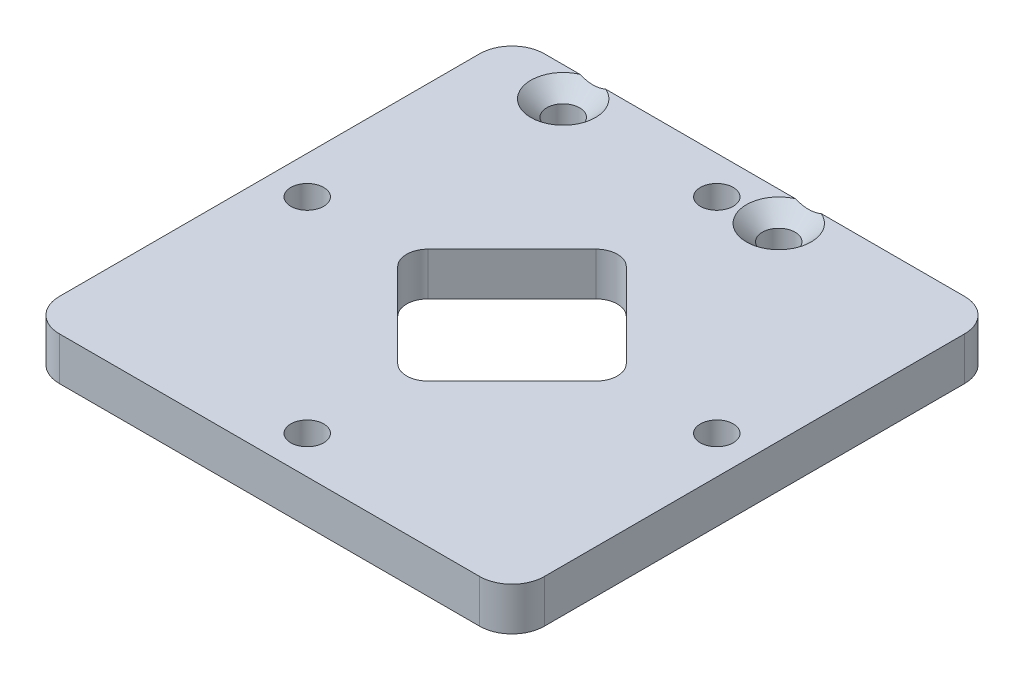
SolidWorks part; units mm, degrees
material "Thornel Mat VMA"
ref_plane "前视基准面" through (0, 0, 0) normal (0, 0, 1) x (1, 0, 0)
ref_plane "上视基准面" through (0, 0, 0) normal (0, 1, 0) x (1, 0, 0)
ref_plane "右视基准面" through (0, 0, 0) normal (1, 0, 0) x (0, 0, -1)
other "Configuration Table"
sketch "草图1" plane through (0, 0, 0) normal (0, 1, 0) x (1, 0, 0)
  line L1 (-22.5, -22.5) -> (22.5, -22.5)
  line L2 (-22.5, -22.5) -> (-22.5, 22.5)
  line L3 (-22.5, 22.5) -> (22.5, 22.5)
  line L4 (22.5, -22.5) -> (22.5, 22.5)
  line L5 (-22.5, -22.5) -> (22.5, 22.5) construction
  line L6 (-22.5, 22.5) -> (22.5, -22.5) construction
  point P0 (0, 0)
  dimension "D1" = 45
  dimension "D2" = 45
extrude "凸台-拉伸1" add sketch "草图1" along normal blind 4
sketch "草图2" plane through (0, 4, 0) normal (0, 1, 0) x (1, 0, 0)
  line L0 (0, 0) -> (0, -22.5) construction
  line L1 (-22.5, -22.5) -> (22.5, -22.5) construction
  circle A0 centre (-19, 0) radius 1.525
  circle A1 centre (19, 0) radius 1.525
  dimension "D1" = 3.05
  dimension "D2" = 38
extrude "切除-拉伸1" cut sketch "草图2" against normal blind 4
fillet "圆角1" radius 3 4 edges at (-22.5, 2, 22.5) (-22.5, 2, -22.5) (22.5, 2, -22.5) (22.5, 2, 22.5)
sketch "草图3" plane through (0, 4, 0) normal (0, 1, 0) x (1, 0, 0)
  circle A0 centre (5, 19.75) radius 1.525
  circle A1 centre (-15, 19.75) radius 1.525
  circle A2 centre (-15, 19.75) radius 1.25 construction
  circle A3 centre (5, 19.75) radius 1.25 construction
  dimension "D1" = 3.05
hole_wizard "孔1" positions "3D草图1" profile "草图4" legacy end condition through all
sketch3d "3D草图1"
  point P0 (-15, 4, -19.75)
  point P3 (5, 4, -19.75)
sketch "草图4" plane through (-15, 4, -19.75) normal (1, 0, 0) x (0, 0, 1)
  line L0 (0, 0) -> (0, 4)
  line L1 (0, 4) -> (1.5, 4)
  line L2 (1.5, 4) -> (1.5, 1.5)
  line L3 (1.5, 1.5) -> (3, 0)
  line L4 (3, 0) -> (0, 0)
  line L5 (0, -6.4453) -> (0, 115.525) construction
  line L6 (-1.5, 1.5) -> (-3, 0) construction
  dimension "直径" = 3
  dimension "深度" = 4
  dimension "锥坑角度" = 90
  dimension "锥坑直径" = 6
sketch "草图5" plane through (0, 4, 0) normal (0, 1, 0) x (1, 0, 0)
  line L0 (0, 0) -> (19, 0) construction
  circle A0 centre (0, 19) radius 1.525
  circle A1 centre (0, -19) radius 1.525
  dimension "D1" = 38
  dimension "D2" = 3.05
extrude "切除-拉伸2" cut sketch "草图5" against normal blind 10
hole_wizard "孔2" positions "草图6" profile "草图7" legacy end condition through all
sketch "草图6" plane through (0, 0, 0) normal (0, -1, 0) x (-1, 0, 0)
  point P0 (0, 19)
sketch "草图7" plane through (0, 0, -19) normal (1, 0, 0) x (0, 0, -1)
  line L0 (0, 0) -> (0, 4)
  line L1 (0, 4) -> (1.5, 4)
  line L2 (1.5, 4) -> (1.5, 1.5)
  line L3 (1.5, 1.5) -> (3, 0)
  line L4 (3, 0) -> (0, 0)
  line L5 (0, -6.4453) -> (0, 115.525) construction
  line L6 (-1.5, 1.5) -> (-3, 0) construction
  dimension "直径" = 3
  dimension "深度" = 4
  dimension "锥坑角度" = 90
  dimension "锥坑直径" = 6
sketch "草图8" plane through (0, 4, 0) normal (0, 1, 0) x (1, 0, 0)
  line L1 (0, 10.6066) -> (-10.6066, 0)
  line L2 (-10.6066, 0) -> (0, -10.6066)
  line L3 (0, -10.6066) -> (10.6066, 0)
  line L4 (10.6066, 0) -> (0, 10.6066)
  circle A0 centre (0, 0) radius 7.5 construction
  point P1 (0, 0)
  dimension "D1" = 15
extrude "切除-拉伸3" cut sketch "草图8" against normal through all both
fillet "圆角2" radius 2 4 edges at (10.6066, 2, 0) (0, 2, 10.6066) (0, 2, -10.6066) (-10.6066, 2, 0)
extrude "切除-拉伸4" cut sketch "草图3" against normal through all both
